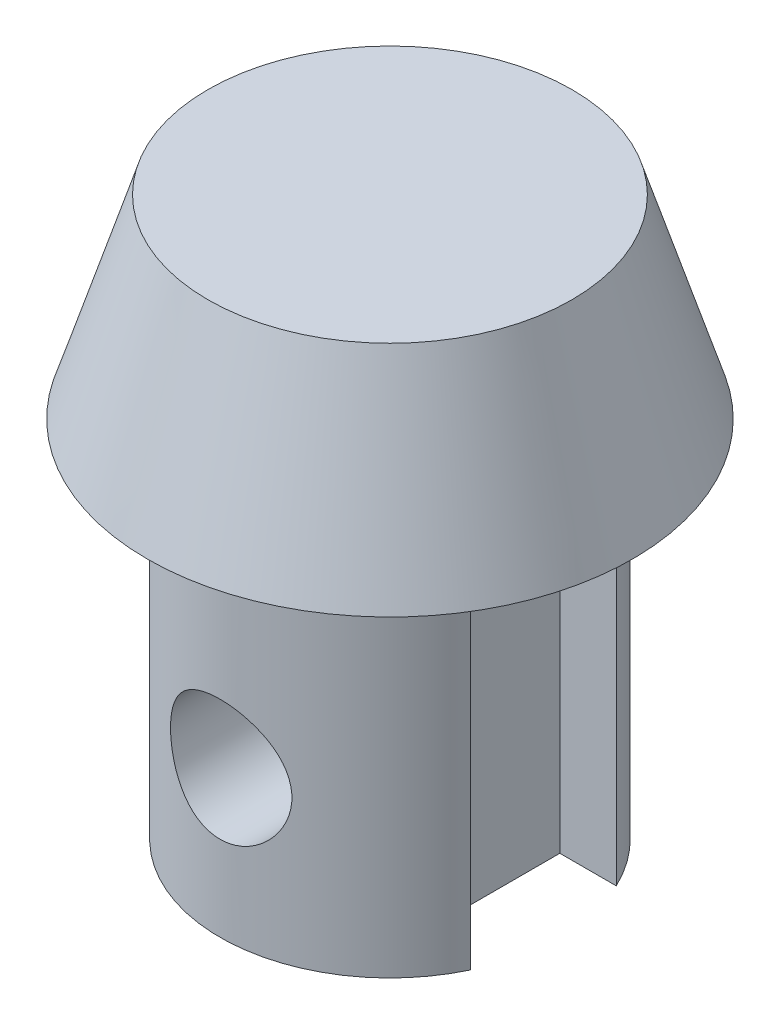
SolidWorks part; units mm, degrees
ref_plane "Front Plane" through (0, 0, 0) normal (0, 0, 1) x (1, 0, 0)
ref_plane "Top Plane" through (0, 0, 0) normal (0, 1, 0) x (1, 0, 0)
ref_plane "Right Plane" through (0, 0, 0) normal (1, 0, 0) x (0, 0, -1)
sketch "Sketch1" plane through (0, 0, 0) normal (0, 1, 0) x (1, 0, 0)
  line L0 (0, 0) -> (6.4771, 0) construction
  line L1 (-6.3246, -3) -> (-4, -3)
  line L3 (-6.3246, 3) -> (-4, 3)
  line L5 (4, 3) -> (6.3246, 3)
  line L7 (-4, -3) -> (-4, 3)
  line L9 (4, -3) -> (4, 3)
  line L10 (-4, -3) -> (4, 3) construction
  line L11 (-4, 3) -> (4, -3) construction
  line L12 (4, -3) -> (6.3246, -3)
  arc A0 (-6.3246, -3) -> (6.3246, -3) centre (0, 0) ccw
  arc A1 (6.3246, 3) -> (-6.3246, 3) centre (0, 0) ccw
  dimension "D1" = 14
  dimension "D2" = 6
  dimension "D3" = 8
extrude "Boss-Extrude1" add sketch "Sketch1" along normal blind 15
sketch "Sketch2" plane through (0, 15, 0) normal (0, 1, 0) x (1, 0, 0)
  circle A0 centre (0, 0) radius 10
  dimension "D1" = 20
ref_plane "Plane1" through (0, 23, 0) normal (0, 1, 0) x (1, 0, 0)
sketch "Sketch3" plane through (0, 23, 0) normal (0, 1, 0) x (1, 0, 0)
  circle A0 centre (0, 0) radius 7.5
  dimension "D1" = 15
loft "Loft1" add profiles "Sketch3", "Sketch2"
ref_plane "Plane2" through (0, 0, -11) normal (0, 0, 1) x (1, 0, 0)
sketch "Sketch4" plane through (0, 0, -11) normal (0, 0, 1) x (1, 0, 0)
  line L0 (-6.3246, 0) -> (6.3246, 0) construction
  circle A0 centre (0, 6) radius 2.5
  point P4 (0, 0)
  dimension "D1" = 6
  dimension "D2" = 5
extrude "Cut-Extrude1" cut sketch "Sketch4" against normal through all both and the other way through all
